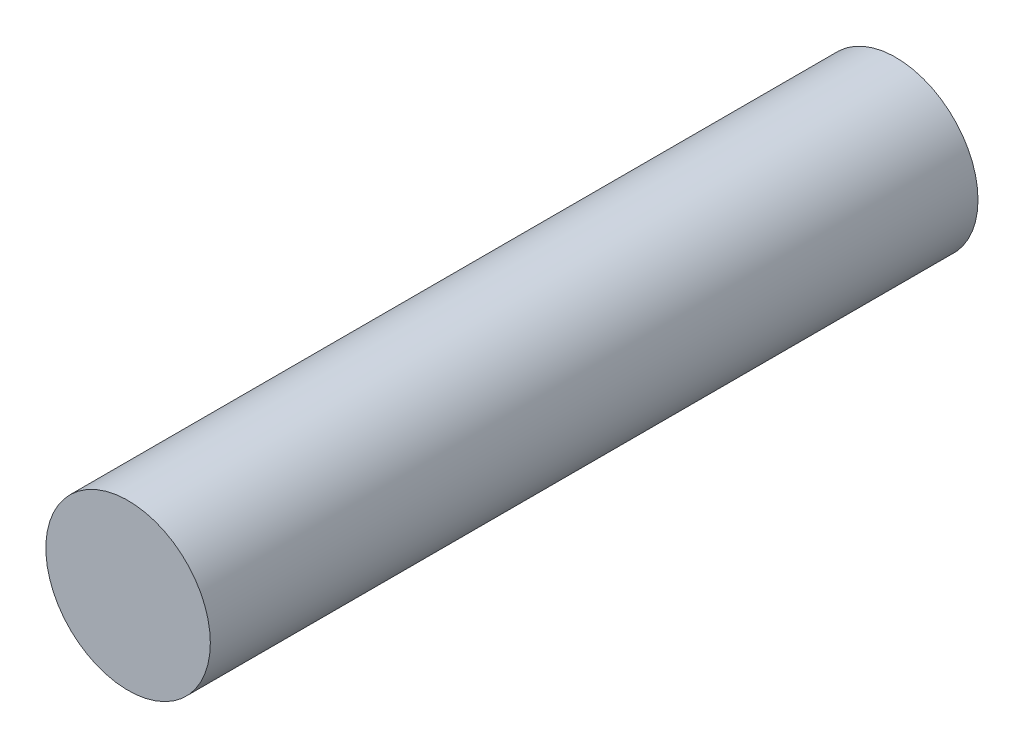
SolidWorks part; units mm, degrees
ref_plane "Alzado" through (0, 0, 0) normal (0, 0, 1) x (1, 0, 0)
ref_plane "Planta" through (0, 0, 0) normal (0, 1, 0) x (1, 0, 0)
ref_plane "Vista lateral" through (0, 0, 0) normal (1, 0, 0) x (0, 0, -1)
sketch "Croquis5" plane through (0, 0, 0) normal (0, 0, 1) x (1, 0, 0)
  circle A0 centre (0, 0) radius 3
  dimension "D1" = 6
extrude "Saliente-Extruir5" add sketch "Croquis5" along normal blind 28
scale "Escala1" scale about centroid uniform scaling yes scale factor 7
scale "Escala2" scale about centroid uniform scaling yes scale factor 7
